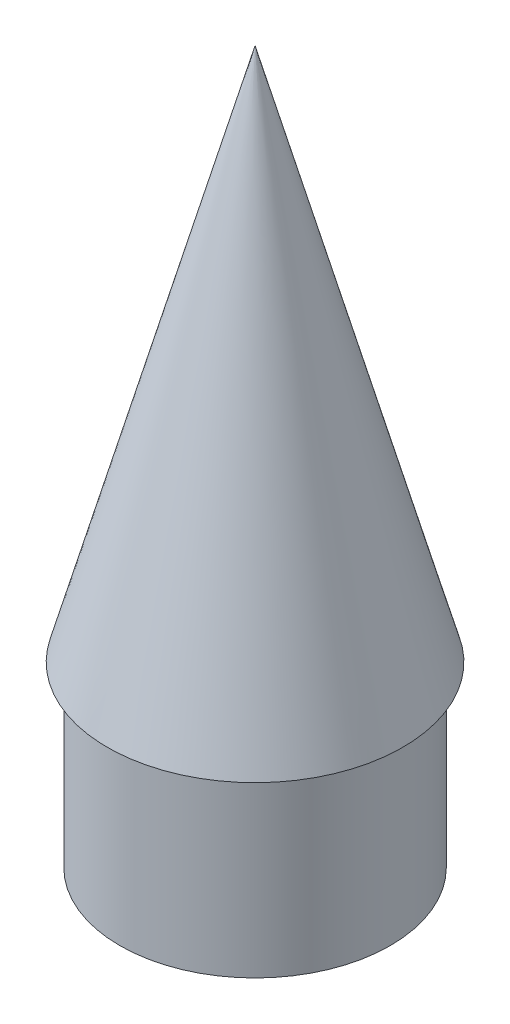
SolidWorks part; units mm, degrees
ref_plane "Front Plane" through (0, 0, 0) normal (0, 0, 1) x (1, 0, 0)
ref_plane "Top Plane" through (0, 0, 0) normal (0, 1, 0) x (1, 0, 0)
ref_plane "Right Plane" through (0, 0, 0) normal (1, 0, 0) x (0, 0, -1)
sketch "Sketch1" plane through (0, 0, 0) normal (0, 0, 1) x (1, 0, 0)
  line L1 (0, 150) -> (-41.5, 0)
  line L2 (-41.5, 0) -> (-33, 0)
  line L3 (0, 142.4995) -> (-38.8715, 2)
  line L4 (-38.8715, 2) -> (-33, 2)
  line L6 (0, 142.4995) -> (0, 150)
  line L7 (0, 2) -> (0, 142.4995) construction
  line L8 (-33, 2) -> (-33, 0)
  line L9 (0, 0) -> (-25.623, 0) construction
  dimension "D1" = 41.5
  dimension "D2" = 150
  dimension "D3" = 2
  dimension "D4" = 2
  dimension "D5" = 2
  dimension "D6" = 2
  dimension "D7" = 33
revolve "Revolve3" add sketch "Sketch1" angle 360 about L7
sketch "Sketch2" plane through (0, 0, 0) normal (0, 0, 1) x (1, 0, 0)
  line L0 (33, 30.7229) -> (33, -50)
  line L1 (41.5, 0) -> (0, 150) construction
  line L2 (33, -50) -> (38, -50)
  line L3 (38, -50) -> (38, 0)
  line L5 (0, 0) -> (0, -76.9883) construction
  line L6 (-41.5, 0) -> (41.5, 0) construction
  line L7 (-41.5, 0) -> (33, 0) construction
  line L8 (41.5, 0) -> (0, 150)
  line L9 (33, 30.7229) -> (38, 12.6506)
  line L10 (33, 30.7229) -> (41.5, 0)
  line L11 (38, 0) -> (41.5, 0)
  line L12 (33, 0) -> (38, 0) construction
  dimension "D1" = 38
  dimension "D2" = 5
  dimension "D3" = 50
revolve "Revolve6" add sketch "Sketch2" angle 360 about L5
ref_plane "Plane1" through (0, 149.9, 0) normal (0, 1, 0) x (1, 0, 0)
sketch "Sketch4" plane through (0, 149.9, 0) normal (0, 1, 0) x (1, 0, 0)
  line L1 (-24.8746, 25.652) -> (25.4576, 25.652)
  line L2 (-24.8746, 25.652) -> (-24.8746, -21.9596)
  line L3 (-24.8746, -21.9596) -> (25.4576, -21.9596)
  line L4 (25.4576, 25.652) -> (25.4576, -21.9596)
extrude "Cut-Extrude1" cut sketch "Sketch4" along normal blind 10
